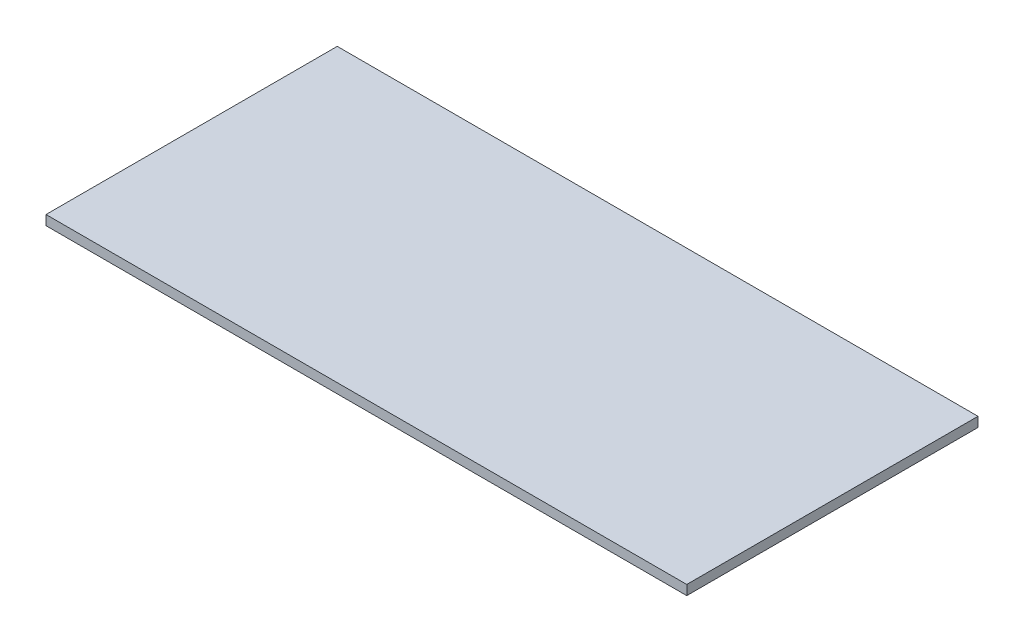
SolidWorks part; units mm, degrees
ref_plane "Front Plane" through (0, 0, 0) normal (0, 0, 1) x (1, 0, 0)
ref_plane "Top Plane" through (0, 0, 0) normal (0, 1, 0) x (1, 0, 0)
ref_plane "Right Plane" through (0, 0, 0) normal (1, 0, 0) x (0, 0, -1)
sketch "Sketch1" plane through (0, 0, 0) normal (0, 1, 0) x (1, 0, 0)
  line L1 (0, 0) -> (83.82, 0)
  line L2 (0, 0) -> (0, -38.1)
  line L3 (0, -38.1) -> (83.82, -38.1)
  line L4 (83.82, 0) -> (83.82, -38.1)
extrude "Boss-Extrude1" add sketch "Sketch1" along normal blind 1.27
